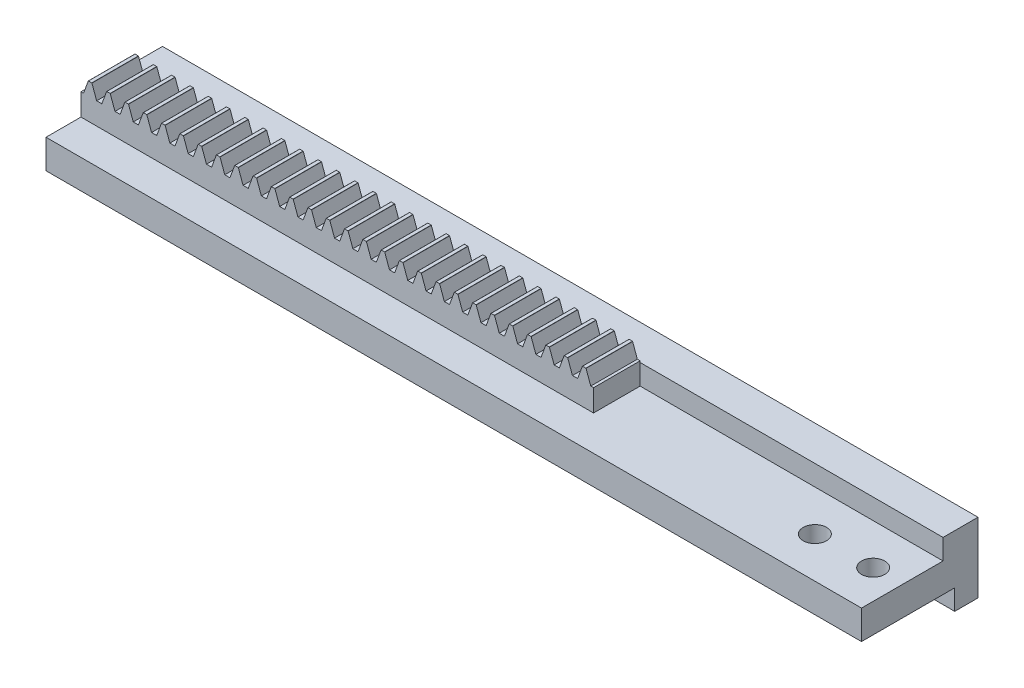
SolidWorks part; units mm, degrees
extrude "Blank" add sketch "BlankSke" against normal blind 4
sketch "BlankSke" plane through (0, 0, 0) normal (0, 0, 1) x (1, 0, 0)
  line L1 (0, 0) -> (70, 0)
  line L2 (0, 0) -> (0, 3.5)
  line L3 (0, 3.5) -> (70, 3.5)
  line L4 (70, 0) -> (70, 3.5)
  dimension "Blank_height" = 3.5
  dimension "D1" = 70
ref_plane "Plane1" through (0, 0, 0) normal (0, 0, 1) x (1, 0, 0)
ref_plane "Plane2" through (0, 0, 0) normal (0, 1, 0) x (1, 0, 0)
ref_plane "Plane3" through (0, 0, 0) normal (1, 0, 0) x (0, 0, -1)
other "Configuration Table"
sketch "HoldingSke" plane through (0, 0, 0) normal (0, 1, 0) x (1, 0, 0)
  line L0 (0, 0) -> (0.2783, 1.9805)
  line L1 (-15, 0) -> (100, 0) construction
  line L2 (0, 0) -> (-2.1039, 2.3779)
  line L3 (0, 0) -> (-11.863, 4.5341)
  line L4 (0, 0) -> (7.2428, 4.7035)
  line L5 (0, 0) -> (-23.7986, -8.8762)
  line L6 (0, 0) -> (-10.5278, -7.1032)
  line L9 (-71.009, 38.7566) -> (-24.0243, 55.8576)
  line L10 (-76.2, 2.8779) -> (-73.2, 2.8779)
  line L11 (0, 0) -> (-4, 0)
  line L12 (-76.2, 101.6) -> (-76.181, 101.6)
  line L13 (24.9733, 27.94) -> (52.9518, 28.4284)
  line L14 (24.9733, 27.94) -> (24.9743, 27.94)
  line L15 (24.9733, 27.94) -> (100.4006, 29.5858)
  circle A0 centre (0, 0) radius 19.05
  circle A1 centre (0, 0) radius 1.5
  circle A2 centre (0, 0) radius 12.7
  dimension "MPH" = 3
  dimension "Diameter" = 38.1
  dimension "Num_teeth" = 33
  dimension "Pitch" = 2
  dimension "Show_teeth" = 998
  dimension "Thickness" = 12.7
  dimension "Ap" = 20
  dimension "Pitch_height" = 3
  dimension "Width" = 4
  dimension "Backlash" = 0.019
  dimension "Addendum_fac" = 1
  dimension "Dedendum_fac" = 1.25
  dimension "Clearance_fac" = 0.25
  dimension "Dedendum_add" = 0.001
  dimension "Length" = 50
  dimension "Module" = 0.5
sketch "TooCutSkeIll" plane through (0, 0, 0) normal (0, 0, 1) x (1, 0, 0)
  line L0 (-0.6269, 3.4868) -> (-0.2524, 2.4579)
  line L1 (-0.134, 2.375) -> (0.134, 2.375)
  line L2 (0.2524, 2.4579) -> (0.6269, 3.4868)
  line L3 (70, 3.5) -> (0, 3.5) construction
  line L4 (0, 0) -> (0, 64.897) construction
  line L5 (-13.208, 3) -> (12.954, 3) construction
  line L6 (0, 0) -> (70, 0) construction
  line L7 (0.4497, 3) -> (0.4497, 48.7463) construction
  line L8 (-0.4497, 3) -> (-0.4497, 48.7463) construction
  line L9 (0.6457, 3.5) -> (0.6457, 3.5254)
  line L10 (-0.6457, 3.5) -> (-0.6457, 3.5254)
  line L11 (-0.6457, 3.5254) -> (0.6457, 3.5254)
  arc A0 (0.134, 2.375) -> (0.2524, 2.4579) centre (0.134, 2.501) ccw
  arc A1 (-0.2524, 2.4579) -> (-0.134, 2.375) centre (-0.134, 2.501) ccw
  arc A2 (0.6457, 3.5) -> (0.6269, 3.4868) centre (0.6457, 3.48) ccw
  arc A3 (-0.6269, 3.4868) -> (-0.6457, 3.5) centre (-0.6457, 3.48) ccw
  dimension "Pitch_height" = 3
  dimension "Addendum_plus" = 0.5254
  dimension "Pressure_angle" = 20
  dimension "Gap_width" = 0.8994
  dimension "Dedendum" = 0.625
extrude "ToothCutIll" cut sketch "TooCutSkeIll" against normal through all
sketch "TooCutSkeSim" plane through (0, 0, 0) normal (0, 0, 1) x (1, 0, 0)
  line L0 (0.2222, 2.375) -> (-0.2222, 2.375)
  line L1 (0.6409, 3.5254) -> (0.2222, 2.375)
  line L2 (0, 17.4625) -> (0, 53.467) construction
  line L3 (0.6409, 3.5254) -> (-0.6409, 3.5254)
  line L4 (-0.4497, 3) -> (70, 3) construction
  line L5 (70, 0) -> (70, 3.5) construction
  line L6 (-0.6409, 3.5254) -> (-0.2222, 2.375)
  line L9 (-0.4497, 3) -> (0.4497, 3) construction
  line L10 (0, 0) -> (70, 0) construction
  line L11 (0.4497, 3) -> (0.4497, 53.467) construction
  line L12 (-0.4497, 3) -> (-0.4497, 53.467) construction
  dimension "Pitch_height" = 3
  dimension "Addendum_plus" = 0.5254
  dimension "Pressure_angle" = 20
  dimension "Gap_width" = 0.8994
  dimension "Dedendum" = 0.625
extrude "ToothCutSim" cut sketch "TooCutSkeSim" against normal through all
pattern_linear "TeethCuts" count 33 spacing 1.5708 along (1, 0, 0) of "ToothCutIll", "ToothCutSim"
sketch "Sketch1" plane through (70, 0, 0) normal (1, 0, 0) x (0, 0, -1)
  line L18 (2, 5.5659) -> (2, -2.2742) construction
  line L20 (0, 0.4939) -> (-3, 0.4939)
  line L21 (-3, 0.4939) -> (-3, -2)
  line L22 (-3, -2) -> (0, -2)
  line L23 (4, -2) -> (0, -2)
  line L24 (5, -2) -> (4, -2)
  line L25 (5, -3.7531) -> (5, -2)
  line L26 (7, -3.7531) -> (5, -3.7531)
  line L27 (7, 2.2469) -> (7, -3.7531)
  line L28 (5, 2.2469) -> (7, 2.2469)
  line L29 (5, 0.4939) -> (5, 2.2469)
  line L30 (4, 0.4939) -> (5, 0.4939)
  line L31 (0, 0.4939) -> (4, 0.4939)
  dimension "D1" = 2
extrude "Boss-Extrude1" add sketch "Sketch1" against normal up to surface (70 mm away) up to face at (0, 1.1875, -2)
sketch "Sketch4" plane through (0, 0, -5) normal (0, 0, 1) x (1, 0, 0)
  line L4 (70, 2.2469) -> (0, 2.2469)
  line L5 (0, 2.2469) -> (0, 0.4939)
  line L6 (0, 0.4939) -> (70, 0.4939)
  line L7 (70, 0.4939) -> (70, 2.2469)
  line L8 (70, 2.2469) -> (0, 2.2469)
  line L9 (0, 2.2469) -> (0, 0.4939)
  line L10 (0, 0.4939) -> (70, 0.4939)
  line L11 (70, 0.4939) -> (70, 2.2469)
  dimension "D1" = 0
extrude "Boss-Extrude2" add sketch "Sketch4" along normal up to surface (1 mm away) up to face at (25.7175, 3.0933, -4)
sketch "Sketch2" plane through (70, 0, 0) normal (1, 0, 0) x (0, 0, -1)
  line L0 (0, 0.4939) -> (4, 0.4939)
  line L1 (4, 0.4939) -> (4, 3.5)
  line L2 (4, 3.5) -> (0, 3.5)
  line L3 (0, 3.5) -> (0, 0.4939)
extrude "Cut-Extrude1" cut sketch "Sketch2" against normal blind 26
sketch "Sketch3" plane through (0, 0.4939, 0) normal (0, 1, 0) x (1, 0, 0)
  line L0 (70, 0.5) -> (67.5, 0.5)
  line L1 (70, 4) -> (70, -3) construction
  line L2 (67.5, 0.5) -> (62.5, 0.5)
  circle A0 centre (67.5, 0.5) radius 1
  circle A1 centre (62.5, 0.5) radius 1
  dimension "D3" = 2
  dimension "D4" = 2
  dimension "D1" = 2.5
  dimension "D2" = 5
extrude "Cut-Extrude2" cut sketch "Sketch3" against normal mid plane 15
equation "' \"Module@HoldingSke\" = 6.35"
equation "' \"Num_teeth@HoldingSke\" = 12"
equation "' \"Ap@HoldingSke\" =  20"
equation "' \"Ap@HoldingSke\" = 20"
equation "' \"Width@HoldingSke\" = 0.25 * 25.4"
equation "' \"Show_teeth@HoldingSke\" = 500"
equation "' \"Backlash@HoldingSke\" = 0.009 * 25.4"
equation "' \"Addendum_fac@HoldingSke\" = 1.0"
equation "' \"Dedendum_fac@HoldingSke\" = 1.25"
equation "' \"Dedendum_add@HoldingSke\" = 0.00005 * 25.4"
equation "' \"Clearance_fac@HoldingSke\" = 0.25"
equation "' \"Pitch_height@HoldingSke\" = 1 * 25.4"
equation "' \"Length@HoldingSke\" = 4.71 * 25.4"
equation "\"Pitch@HoldingSke\" = 1 / \"Module@HoldingSke\""
equation "\"MPH@HoldingSke\" = \"Dedendum_fac@HoldingSke\" / \"Pitch@HoldingSke\" + 2 * \"Dedendum_add@HoldingSke\" + 0.002 * 25.4"
equation "\"MPH@HoldingSke\" = ((sgn( \"MPH@HoldingSke\" - \"Pitch_height@HoldingSke\")+1)*( \"MPH@HoldingSke\" - \"Pitch_height@HoldingSke\"))/2 + \"Pitch_height@HoldingSke\""
equation "\"Blank_height@BlankSke\" = \"Pitch_height@HoldingSke\" + \"Addendum_fac@HoldingSke\"  / \"Pitch@HoldingSke\" "
equation "\"Face_width@Blank\" = \"Width@HoldingSke\""
equation "\"Pressure_angle@TooCutSkeIll\" = \"Ap@HoldingSke\""
equation "\"Addendum_plus@TooCutSkeIll\" =  \"Addendum_fac@HoldingSke\"  / \"Pitch@HoldingSke\" + 0.001 *25.4"
equation "\"Dedendum@TooCutSkeIll\" = \"Dedendum_fac@HoldingSke\"  / \"Pitch@HoldingSke\""
equation "\"Pitch_height@TooCutSkeIll\" =  \"MPH@HoldingSke\""
equation "\"Gap_width@TooCutSkeIll\" = 3.14159265 / 2 / \"Pitch@HoldingSke\" + 6 * \"Backlash@HoldingSke\""
equation "\"Pressure_angle@TooCutSkeSim\" = \"Ap@HoldingSke\""
equation "\"Addendum_plus@TooCutSkeSim\" =  \"Addendum_fac@HoldingSke\"  / \"Pitch@HoldingSke\" + 0.001 * 25.4"
equation "\"Dedendum@TooCutSkeSim\" = \"Dedendum_fac@HoldingSke\"  / \"Pitch@HoldingSke\""
equation "\"Pitch_height@TooCutSkeSim\" =  \"MPH@HoldingSke\""
equation "\"Gap_width@TooCutSkeSim\" = 3.14159265 / 2 / \"Pitch@HoldingSke\" + 6 * \"Backlash@HoldingSke\""
equation "\"Root_fillet@TooCutSkeIll\" = \"Clearance_fac@HoldingSke\" / \"Pitch@HoldingSke\" + \"Dedendum_add@HoldingSke\""
equation "\"Break_rad@TooCutSkeIll\" = 0.02 / \"Pitch@HoldingSke\" * 2"
equation "\"Linear_pitch@TeethCuts\" = 3.14159265 / \"Pitch@HoldingSke\""
equation "\"Num_teeth@HoldingSke\" = int( ( \"Length@HoldingSke\" + 0 ) / (3.14159265 / \"Pitch@HoldingSke\")) + 0.9999  + 1"
equation " \"Num_teeth@TeethCuts\" = int( \"Show_teeth@HoldingSke\" ) + 1"
equation " \"Num_teeth@TeethCuts\" = ((sgn( \"Num_teeth@TeethCuts\" - \"Num_teeth@HoldingSke\" )-1)*( \"Num_teeth@TeethCuts\" - \"Num_teeth@HoldingSke\" ))/-2+ \"Num_teeth@HoldingSke\""
equation " \"Num_teeth@TeethCuts\" = ((sgn( \"Num_teeth@TeethCuts\" - 2.0)+1)*( \"Num_teeth@TeethCuts\" - 2.0))/2 +2.0"
